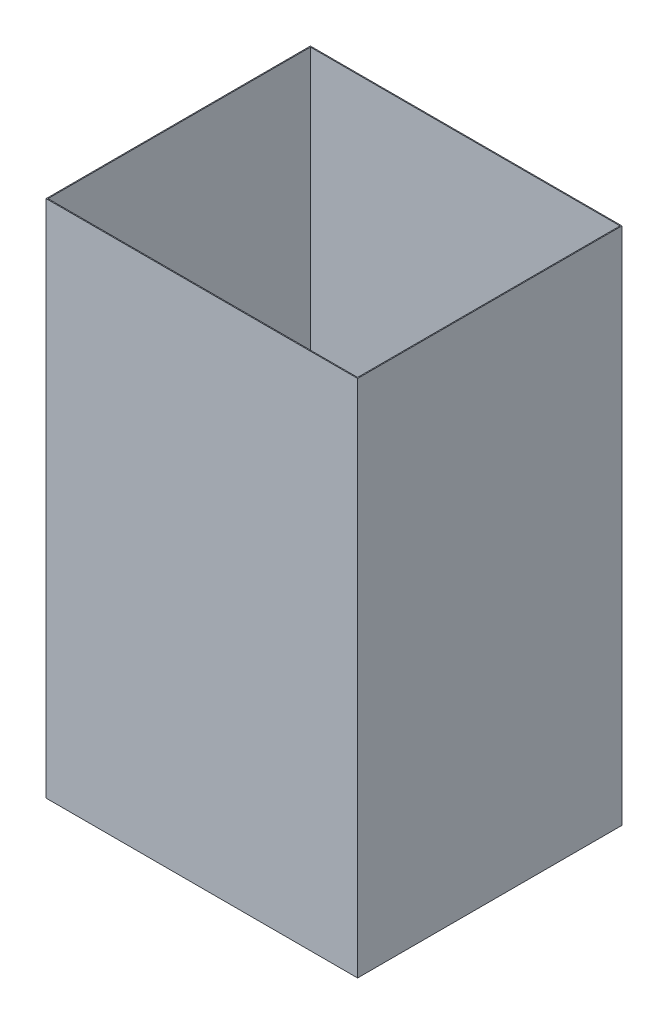
SolidWorks part; units mm, degrees
ref_plane "Front" through (0, 0, 0) normal (0, 0, 1) x (1, 0, 0)
ref_plane "Top" through (0, 0, 0) normal (0, 1, 0) x (1, 0, 0)
ref_plane "Right" through (0, 0, 0) normal (1, 0, 0) x (0, 0, -1)
sketch "Sketch1" plane through (0, 0, 0) normal (0, 1, 0) x (1, 0, 0)
  line L1 (0, 0) -> (838.2, 0)
  line L2 (0, 0) -> (0, 711.2)
  line L3 (0, 711.2) -> (838.2, 711.2)
  line L4 (838.2, 0) -> (838.2, 711.2)
  line L5 (0, 0) -> (838.2, 711.2) construction
  line L6 (0, 711.2) -> (838.2, 0) construction
  point P4 (419.1, 355.6)
  dimension "D1" = 711.2
  dimension "D2" = 838.2
extrude "Boss-Extrude1" add sketch "Sketch1" along normal blind 1397
shell "Shell1" thickness 2.54
ref_plane "Max_Bumper_Height" through (0, 177.8, 0) normal (0, 1, 0) x (1, 0, 0)
sketch "Sketch2" plane through (0, 1394.46, 0) normal (0, -1, 0) x (1, 0, 0)
  line L4 (2.54, -2.54) -> (2.54, -708.66)
  line L5 (2.54, -708.66) -> (835.66, -708.66)
  line L6 (835.66, -708.66) -> (835.66, -2.54)
  line L7 (835.66, -2.54) -> (2.54, -2.54)
  line L8 (2.54, -2.54) -> (2.54, -708.66)
  line L9 (2.54, -708.66) -> (835.66, -708.66)
  line L10 (835.66, -708.66) -> (835.66, -2.54)
  line L11 (835.66, -2.54) -> (2.54, -2.54)
  dimension "D1" = 0
extrude "Cut-Extrude1" cut sketch "Sketch2" against normal up to next
